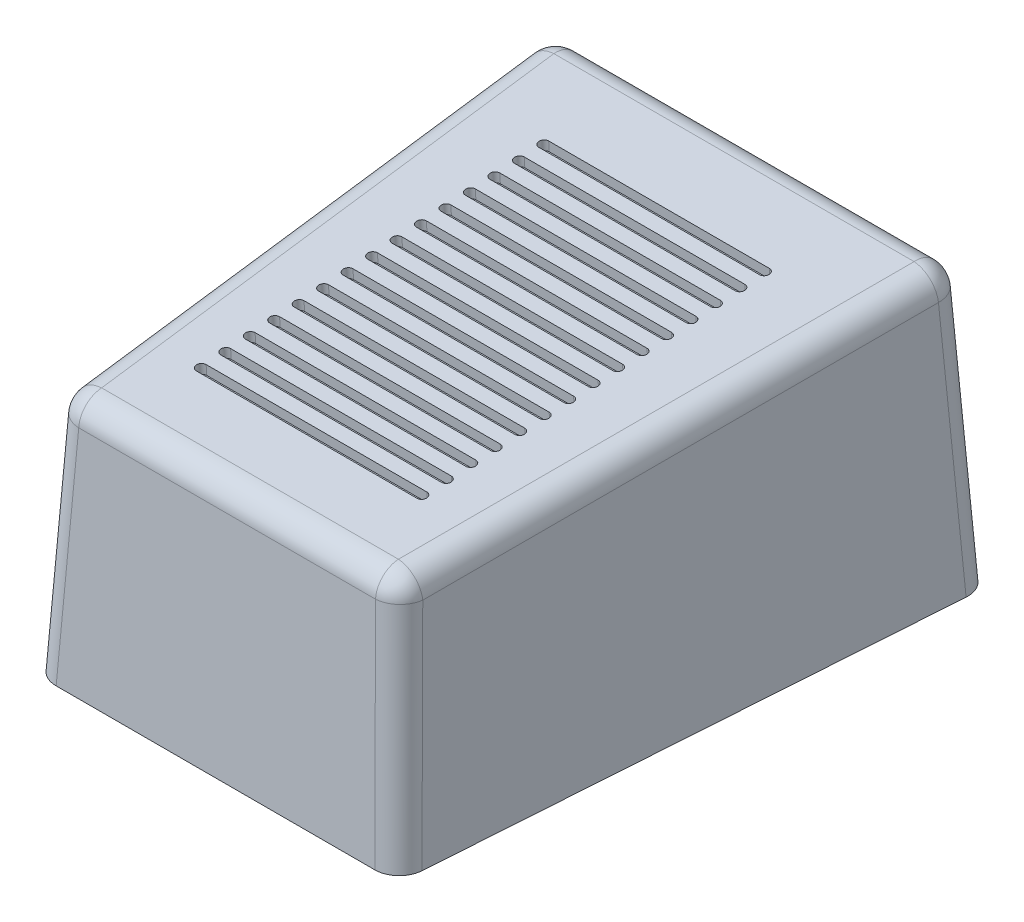
SolidWorks part; units mm, degrees
material "ABS"
ref_plane "Front Plane" through (0, 0, 0) normal (0, 0, 1) x (1, 0, 0)
ref_plane "Top Plane" through (0, 0, 0) normal (0, 1, 0) x (1, 0, 0)
ref_plane "Right Plane" through (0, 0, 0) normal (1, 0, 0) x (0, 0, -1)
sketch "Sketch1" plane through (0, 0, 0) normal (0, 1, 0) x (1, 0, 0)
  line L0 (0, 0) -> (74.3, 0)
  line L4 (0, 0) -> (-7.85, 113.7899)
  line L5 (-7.85, 113.7899) -> (82.15, 113.7899)
  line L6 (82.15, 113.7899) -> (74.3, 0)
  dimension "D1" = 90
  dimension "D2" = 74.3
extrude "Boss-Extrude1" add sketch "Sketch1" along normal blind 57 draft 3 contours L4 L5 L6 L0
sketch "Sketch3" plane through (0, 0, 0) normal (-0.9963, 0.0523, 0.0687) x (0.0686, -0.0036, 0.9976)
  line L0 (-111.0653, 56.6776) -> (-2.9943, 57.0678)
  line L1 (-2.9943, 57.0678) -> (-2.623, 49.9909)
  line L2 (-2.9943, 57.0678) -> (0, 0) construction
  line L3 (-2.623, 49.9909) -> (-111.0653, 56.6776)
  line L4 (0, 0) -> (-114.0596, -0.4118) construction
  dimension "D1" = 50
extrude "Cut-Extrude5" cut sketch "Sketch3" along direction (-1, 0, 0) on the side against the normal through all
fillet "Fillet1" radius 5 8 edges at (37.15, 49.9315, -2.6168) (-1.1035, 53.4657, -56.7097) (37.15, 57, -110.8027) (75.4035, 53.4657, -56.7097) (80.5498, 28.5, -112.2963) (-6.2498, 28.5, -112.2963) (73.0788, 24.9657, -1.3084) (1.2212, 24.9657, -1.3084)
sketch "Sketch4" plane through (0, 49.549, 3.2374) normal (0, 0.9979, 0.0652) x (1, 0, 0)
  line L0 (14.3292, 93.21) -> (59.3292, 93.21) construction
  line L1 (14.3292, 94.21) -> (59.3292, 94.21)
  line L2 (14.3292, 92.21) -> (59.3292, 92.21)
  line L3 (14.3292, 88.21) -> (59.3292, 88.21) construction
  line L4 (14.3292, 89.21) -> (59.3292, 89.21)
  line L5 (14.3292, 87.21) -> (59.3292, 87.21)
  line L6 (14.3292, 83.21) -> (59.3292, 83.21) construction
  line L7 (14.3292, 84.21) -> (59.3292, 84.21)
  line L8 (14.3292, 82.21) -> (59.3292, 82.21)
  line L9 (14.3292, 78.21) -> (59.3292, 78.21) construction
  line L10 (14.3292, 79.21) -> (59.3292, 79.21)
  line L11 (14.3292, 77.21) -> (59.3292, 77.21)
  line L12 (14.3292, 73.21) -> (59.3292, 73.21) construction
  line L13 (14.3292, 74.21) -> (59.3292, 74.21)
  line L14 (14.3292, 72.21) -> (59.3292, 72.21)
  line L15 (14.3292, 68.21) -> (59.3292, 68.21) construction
  line L16 (14.3292, 69.21) -> (59.3292, 69.21)
  line L17 (14.3292, 67.21) -> (59.3292, 67.21)
  line L18 (14.3292, 63.21) -> (59.3292, 63.21) construction
  line L19 (14.3292, 64.21) -> (59.3292, 64.21)
  line L20 (14.3292, 62.21) -> (59.3292, 62.21)
  line L21 (14.3292, 58.21) -> (59.3292, 58.21) construction
  line L22 (14.3292, 59.21) -> (59.3292, 59.21)
  line L23 (14.3292, 57.21) -> (59.3292, 57.21)
  line L24 (14.3292, 53.21) -> (59.3292, 53.21) construction
  line L25 (14.3292, 54.21) -> (59.3292, 54.21)
  line L26 (14.3292, 52.21) -> (59.3292, 52.21)
  line L27 (14.3292, 48.21) -> (59.3292, 48.21) construction
  line L28 (14.3292, 49.21) -> (59.3292, 49.21)
  line L29 (14.3292, 47.21) -> (59.3292, 47.21)
  line L30 (14.3292, 43.21) -> (59.3292, 43.21) construction
  line L31 (14.3292, 44.21) -> (59.3292, 44.21)
  line L32 (14.3292, 42.21) -> (59.3292, 42.21)
  line L33 (14.3292, 38.21) -> (59.3292, 38.21) construction
  line L34 (14.3292, 39.21) -> (59.3292, 39.21)
  line L35 (14.3292, 37.21) -> (59.3292, 37.21)
  line L36 (14.3292, 33.21) -> (59.3292, 33.21) construction
  line L37 (14.3292, 34.21) -> (59.3292, 34.21)
  line L38 (14.3292, 32.21) -> (59.3292, 32.21)
  line L39 (14.3292, 28.21) -> (59.3292, 28.21) construction
  line L40 (14.3292, 29.21) -> (59.3292, 29.21)
  line L41 (14.3292, 27.21) -> (59.3292, 27.21)
  line L42 (14.3292, 23.21) -> (59.3292, 23.21) construction
  line L43 (14.3292, 24.21) -> (59.3292, 24.21)
  line L44 (14.3292, 22.21) -> (59.3292, 22.21)
  arc A0 (14.3292, 94.21) -> (14.3292, 92.21) centre (14.3292, 93.21) ccw
  arc A1 (59.3292, 92.21) -> (59.3292, 94.21) centre (59.3292, 93.21) ccw
  arc A2 (14.3292, 89.21) -> (14.3292, 87.21) centre (14.3292, 88.21) ccw
  arc A3 (59.3292, 87.21) -> (59.3292, 89.21) centre (59.3292, 88.21) ccw
  arc A4 (14.3292, 84.21) -> (14.3292, 82.21) centre (14.3292, 83.21) ccw
  arc A5 (59.3292, 82.21) -> (59.3292, 84.21) centre (59.3292, 83.21) ccw
  arc A6 (14.3292, 79.21) -> (14.3292, 77.21) centre (14.3292, 78.21) ccw
  arc A7 (59.3292, 77.21) -> (59.3292, 79.21) centre (59.3292, 78.21) ccw
  arc A8 (14.3292, 74.21) -> (14.3292, 72.21) centre (14.3292, 73.21) ccw
  arc A9 (59.3292, 72.21) -> (59.3292, 74.21) centre (59.3292, 73.21) ccw
  arc A10 (14.3292, 69.21) -> (14.3292, 67.21) centre (14.3292, 68.21) ccw
  arc A11 (59.3292, 67.21) -> (59.3292, 69.21) centre (59.3292, 68.21) ccw
  arc A12 (14.3292, 64.21) -> (14.3292, 62.21) centre (14.3292, 63.21) ccw
  arc A13 (59.3292, 62.21) -> (59.3292, 64.21) centre (59.3292, 63.21) ccw
  arc A14 (14.3292, 59.21) -> (14.3292, 57.21) centre (14.3292, 58.21) ccw
  arc A15 (59.3292, 57.21) -> (59.3292, 59.21) centre (59.3292, 58.21) ccw
  arc A16 (14.3292, 54.21) -> (14.3292, 52.21) centre (14.3292, 53.21) ccw
  arc A17 (59.3292, 52.21) -> (59.3292, 54.21) centre (59.3292, 53.21) ccw
  arc A18 (14.3292, 49.21) -> (14.3292, 47.21) centre (14.3292, 48.21) ccw
  arc A19 (59.3292, 47.21) -> (59.3292, 49.21) centre (59.3292, 48.21) ccw
  arc A20 (14.3292, 44.21) -> (14.3292, 42.21) centre (14.3292, 43.21) ccw
  arc A21 (59.3292, 42.21) -> (59.3292, 44.21) centre (59.3292, 43.21) ccw
  arc A22 (14.3292, 39.21) -> (14.3292, 37.21) centre (14.3292, 38.21) ccw
  arc A23 (59.3292, 37.21) -> (59.3292, 39.21) centre (59.3292, 38.21) ccw
  arc A24 (14.3292, 34.21) -> (14.3292, 32.21) centre (14.3292, 33.21) ccw
  arc A25 (59.3292, 32.21) -> (59.3292, 34.21) centre (59.3292, 33.21) ccw
  arc A26 (14.3292, 29.21) -> (14.3292, 27.21) centre (14.3292, 28.21) ccw
  arc A27 (59.3292, 27.21) -> (59.3292, 29.21) centre (59.3292, 28.21) ccw
  arc A28 (14.3292, 24.21) -> (14.3292, 22.21) centre (14.3292, 23.21) ccw
  arc A29 (59.3292, 22.21) -> (59.3292, 24.21) centre (59.3292, 23.21) ccw
  point P2 (36.8292, 93.21)
  point P11 (36.8292, 88.21)
  point P18 (36.8292, 83.21)
  point P25 (36.8292, 78.21)
  point P32 (36.8292, 73.21)
  point P39 (36.8292, 68.21)
  point P46 (36.8292, 63.21)
  point P53 (36.8292, 58.21)
  point P60 (36.8292, 53.21)
  point P67 (36.8292, 48.21)
  point P74 (36.8292, 43.21)
  point P81 (36.8292, 38.21)
  point P88 (36.8292, 33.21)
  point P95 (36.8292, 28.21)
  point P102 (36.8292, 23.21)
  dimension "D1" = 2
  dimension "D2" = 45
  dimension "D3" = 37.15
  dimension "D4" = 15
extrude "Cut-Extrude6" cut sketch "Sketch4" against normal blind 2
sketch "Sketch5" plane through (0, 0, 0) normal (0, 1, 0) x (1, 0, 0)
  line L0 (37.15, 113.7899) -> (37.15, 0) construction
  line L1 (-7.85, 113.7899) -> (82.15, 113.7899) construction
  line L2 (0, 0) -> (74.3, 0) construction
